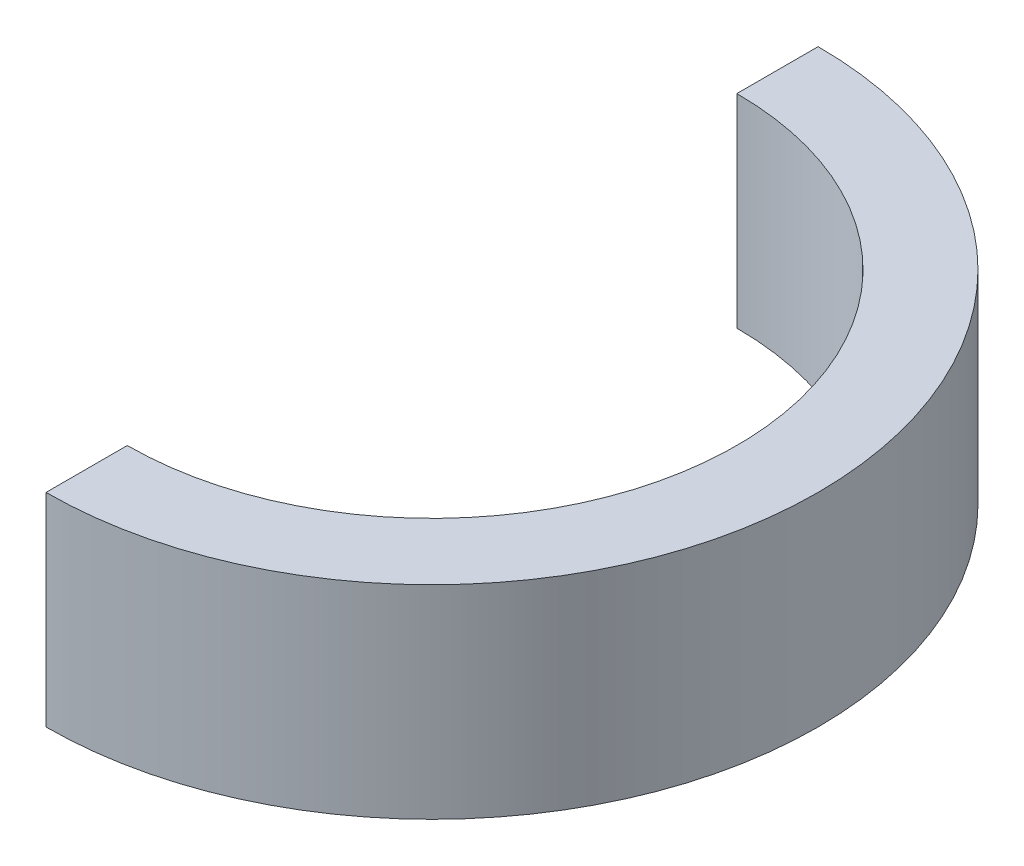
SolidWorks part; units mm, degrees
ref_plane "Front" through (0, 0, 0) normal (0, 0, 1) x (1, 0, 0)
ref_plane "Top" through (0, 0, 0) normal (0, 1, 0) x (1, 0, 0)
ref_plane "Right" through (0, 0, 0) normal (1, 0, 0) x (0, 0, -1)
sketch "草图1" plane through (0, 0, 0) normal (0, 1, 0) x (1, 0, 0)
  line L0 (0, 38) -> (0, 30)
  line L1 (0, -30) -> (0, -38)
  arc A0 (0, -30) -> (0, 30) centre (0, 0) ccw
  arc A1 (0, -38) -> (0, 38) centre (0, 0) ccw
extrude "凸台-拉伸1" add sketch "草图1" along normal blind 20
